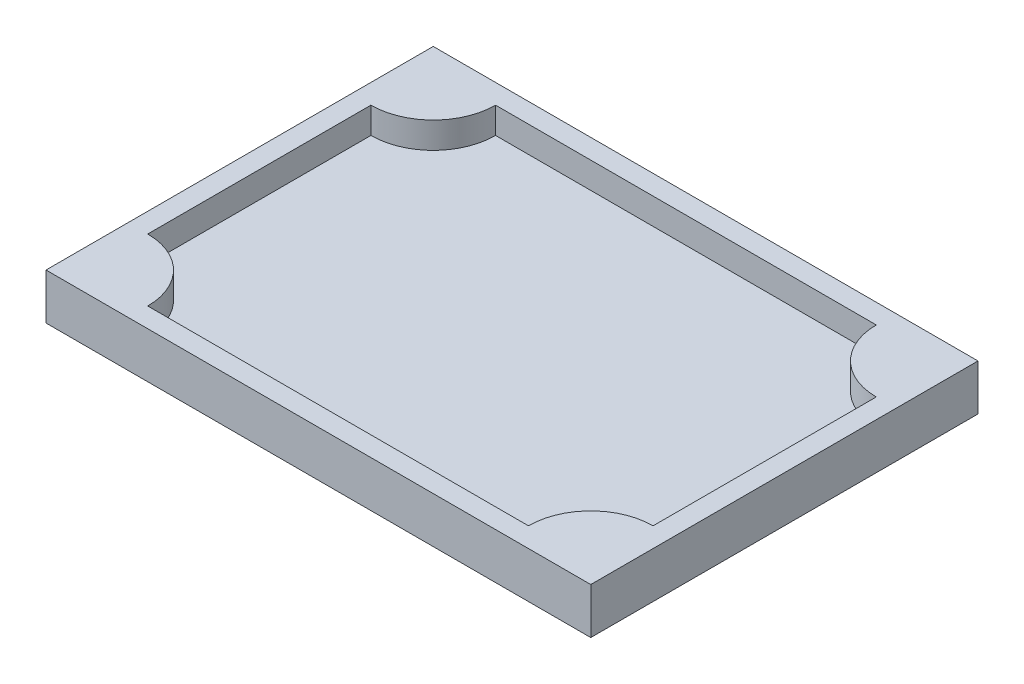
SolidWorks part; units mm, degrees
ref_plane "Front Plane" through (0, 0, 0) normal (0, 0, 1) x (1, 0, 0)
ref_plane "Top Plane" through (0, 0, 0) normal (0, 1, 0) x (1, 0, 0)
ref_plane "Right Plane" through (0, 0, 0) normal (1, 0, 0) x (0, 0, -1)
sketch "Sketch1" plane through (0, 0, 0) normal (0, 1, 0) x (1, 0, 0)
  line L1 (0, 0) -> (83, 0)
  line L2 (0, 0) -> (0, 59)
  line L3 (0, 59) -> (83, 59)
  line L4 (83, 0) -> (83, 59)
  dimension "D1" = 59
  dimension "D2" = 83
extrude "Boss-Extrude1" add sketch "Sketch1" along normal blind 3
sketch "Sketch2" plane through (0, 3, 0) normal (0, 1, 0) x (1, 0, 0)
  line L9 (0, 0) -> (0, 59)
  line L10 (0, 29.5) -> (3, 29.5) construction
  line L11 (3, 46.5) -> (3, 12.5)
  line L13 (0, 59) -> (0, 0) construction
  line L14 (0, 0) -> (83, 0) construction
  line L18 (12.5, 3) -> (70.5, 3)
  line L19 (41.5, 3) -> (41.5, 0) construction
  line L24 (83, 0) -> (0, 0)
  line L25 (41.5, 56) -> (41.5, 59) construction
  line L26 (83, 59) -> (0, 59)
  line L27 (12.5, 56) -> (70.5, 56)
  line L29 (83, 29.5) -> (80, 29.5) construction
  line L32 (80, 46.5) -> (80, 12.5)
  line L33 (83, 0) -> (83, 59)
  line L34 (7.75, 51.25) -> (7.75, 7.75) construction
  line L35 (7.75, 3) -> (12.5, 3) construction
  line L36 (3, 56) -> (7.75, 56) construction
  line L37 (3, 56) -> (3, 51.25) construction
  line L38 (3, 51.25) -> (7.75, 51.25) construction
  line L39 (7.75, 56) -> (7.75, 51.25) construction
  line L40 (3, 3) -> (7.75, 3) construction
  line L41 (3, 3) -> (3, 7.75) construction
  line L42 (3, 7.75) -> (7.75, 7.75) construction
  line L43 (7.75, 3) -> (7.75, 7.75) construction
  arc A4 (3, 12.5) -> (12.5, 3) centre (3, 3) cw
  arc A5 (3, 46.5) -> (12.5, 56) centre (3, 56) ccw
  arc A6 (80, 46.5) -> (70.5, 56) centre (80, 56) cw
  arc A7 (80, 12.5) -> (70.5, 3) centre (80, 3) ccw
  point P21 (0, 29.5)
  point P24 (41.5, 0)
  dimension "D1" = 3
  dimension "D2" = 43.5
extrude "Boss-Extrude2" add sketch "Sketch2" along direction (0, -1, 0) on the side of the normal offset from surface (4 mm away) 7
